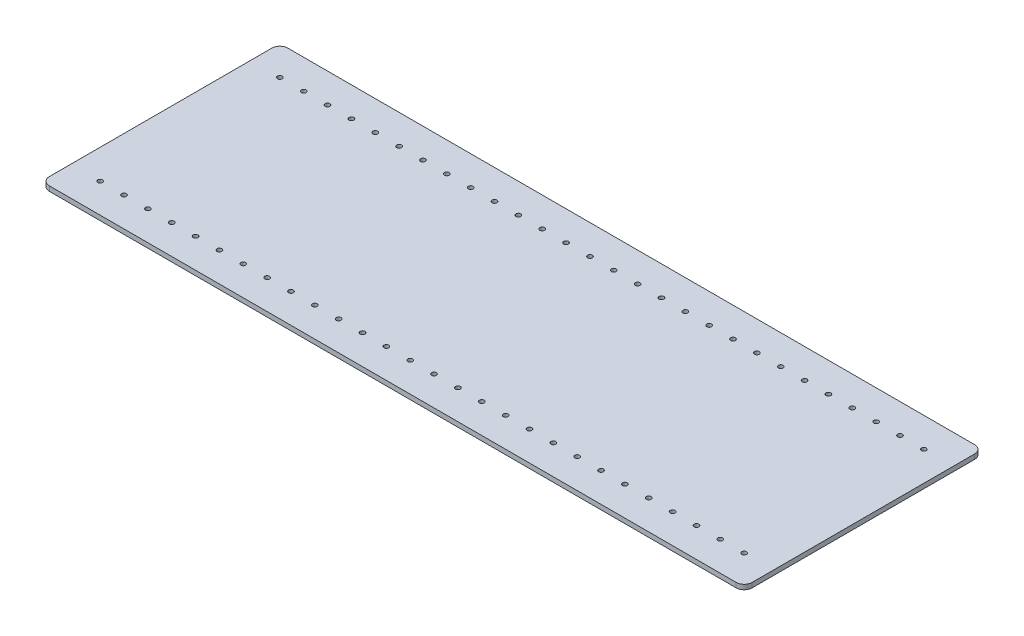
SolidWorks part; units mm, degrees
ref_plane "Front Plane" through (0, 0, 0) normal (0, 0, 1) x (1, 0, 0)
ref_plane "Top Plane" through (0, 0, 0) normal (0, 1, 0) x (1, 0, 0)
ref_plane "Right Plane" through (0, 0, 0) normal (1, 0, 0) x (0, 0, -1)
sketch "Sketch2" plane through (0, 0, 0) normal (0, 1, 0) x (1, 0, 0)
  line L0 (0, 5) -> (0, 145)
  line L1 (5, 0) -> (437, 0)
  line L2 (5, 150) -> (437, 150)
  line L3 (442, 5) -> (442, 145)
  circle A0 centre (18.5, 131.5) radius 1.5
  circle A1 centre (18.5, 18.5) radius 1.5
  circle A2 centre (78.5, 18.5) radius 1.5
  circle A3 centre (63.5, 18.5) radius 1.5
  circle A4 centre (48.5, 18.5) radius 1.5
  circle A5 centre (33.5, 18.5) radius 1.5
  circle A6 centre (78.5, 131.5) radius 1.5
  circle A7 centre (63.5, 131.5) radius 1.5
  circle A8 centre (48.5, 131.5) radius 1.5
  circle A9 centre (33.5, 131.5) radius 1.5
  circle A10 centre (123.5, 131.5) radius 1.5
  circle A11 centre (108.5, 131.5) radius 1.5
  circle A12 centre (93.5, 131.5) radius 1.5
  circle A13 centre (123.5, 18.5) radius 1.5
  circle A14 centre (108.5, 18.5) radius 1.5
  circle A15 centre (93.5, 18.5) radius 1.5
  circle A16 centre (138.5, 18.5) radius 1.5
  circle A17 centre (153.5, 131.5) radius 1.5
  circle A18 centre (138.5, 131.5) radius 1.5
  circle A19 centre (183.5, 131.5) radius 1.5
  circle A20 centre (168.5, 131.5) radius 1.5
  circle A21 centre (183.5, 18.5) radius 1.5
  circle A22 centre (168.5, 18.5) radius 1.5
  circle A23 centre (153.5, 18.5) radius 1.5
  circle A24 centre (198.5, 18.5) radius 1.5
  circle A25 centre (243.5, 18.5) radius 1.5
  circle A26 centre (228.5, 18.5) radius 1.5
  circle A27 centre (213.5, 18.5) radius 1.5
  circle A28 centre (258.5, 18.5) radius 1.5
  circle A29 centre (303.5, 18.5) radius 1.5
  circle A30 centre (288.5, 18.5) radius 1.5
  circle A31 centre (273.5, 18.5) radius 1.5
  circle A32 centre (333.5, 18.5) radius 1.5
  circle A33 centre (318.5, 18.5) radius 1.5
  circle A34 centre (348.5, 18.5) radius 1.5
  circle A35 centre (393.5, 18.5) radius 1.5
  circle A36 centre (378.5, 18.5) radius 1.5
  circle A37 centre (363.5, 18.5) radius 1.5
  circle A38 centre (423.5, 18.5) radius 1.5
  circle A39 centre (408.5, 18.5) radius 1.5
  circle A40 centre (198.5, 131.5) radius 1.5
  circle A41 centre (228.5, 131.5) radius 1.5
  circle A42 centre (213.5, 131.5) radius 1.5
  circle A43 centre (258.5, 131.5) radius 1.5
  circle A44 centre (243.5, 131.5) radius 1.5
  circle A45 centre (288.5, 131.5) radius 1.5
  circle A46 centre (273.5, 131.5) radius 1.5
  circle A47 centre (318.5, 131.5) radius 1.5
  circle A48 centre (303.5, 131.5) radius 1.5
  circle A49 centre (348.5, 131.5) radius 1.5
  circle A50 centre (333.5, 131.5) radius 1.5
  circle A51 centre (378.5, 131.5) radius 1.5
  circle A52 centre (363.5, 131.5) radius 1.5
  circle A53 centre (423.5, 131.5) radius 1.5
  circle A54 centre (408.5, 131.5) radius 1.5
  circle A55 centre (393.5, 131.5) radius 1.5
  arc A56 (5, 150) -> (0, 145) centre (5, 145) ccw
  arc A57 (0, 5) -> (5, 0) centre (5, 5) ccw
  arc A58 (437, 0) -> (442, 5) centre (437, 5) ccw
  arc A59 (442, 145) -> (437, 150) centre (437, 145) ccw
extrude "Boss-Extrude1" add sketch "Sketch2" along normal blind 3
